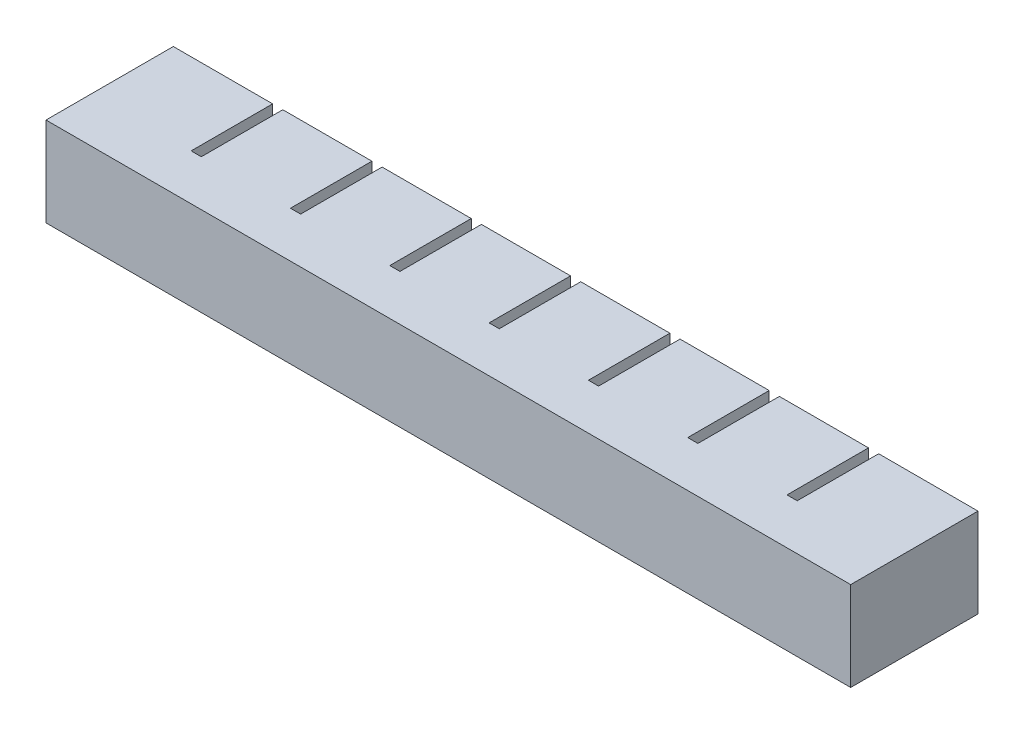
SolidWorks part; units mm, degrees
ref_plane "Front Plane" through (0, 0, 0) normal (0, 0, 1) x (1, 0, 0)
ref_plane "Top Plane" through (0, 0, 0) normal (0, 1, 0) x (1, 0, 0)
ref_plane "Right Plane" through (0, 0, 0) normal (1, 0, 0) x (0, 0, -1)
sketch "Sketch1" plane through (0, 0, 0) normal (0, 0, 1) x (1, 0, 0)
  line L1 (0, 0) -> (17.5, 0)
  line L2 (0, 0) -> (0, 17.5)
  line L3 (0, 17.5) -> (17.5, 17.5)
  line L4 (17.5, 0) -> (17.5, 17.5)
  dimension "D1" = 17.5
  dimension "D2" = 17.5
extrude "Boss-Extrude1" add sketch "Sketch1" along normal blind 20
sketch "Sketch2" plane through (0, 0, 20) normal (0, 0, 1) x (1, 0, 0)
  line L0 (0, 0) -> (17.5, 0) construction
  line L1 (3, 14.5) -> (14.5, 14.5)
  line L2 (3, 14.5) -> (3, 3)
  line L3 (3, 3) -> (14.5, 3)
  line L4 (14.5, 14.5) -> (14.5, 3)
  line L5 (17.5, 0) -> (17.5, 17.5) construction
  line L6 (17.5, 17.5) -> (0, 17.5) construction
  line L7 (0, 17.5) -> (0, 0) construction
  dimension "D1" = 3
  dimension "D2" = 3
  dimension "D3" = 3
  dimension "D4" = 3
extrude "Cut-Extrude1" cut sketch "Sketch2" against normal blind 17
sketch "Sketch4" plane through (0, 0, 0) normal (-1, 0, 0) x (0, 0, 1)
  line L0 (20, 17.5) -> (0, 17.5) construction
  line L1 (20, 0) -> (16, 0)
  line L2 (20, 0) -> (20, 17.5)
  line L3 (20, 17.5) -> (16, 17.5)
  line L4 (16, 0) -> (16, 17.5)
  dimension "D1" = 4
extrude "Boss-Extrude2" add sketch "Sketch4" along normal blind 2
pattern_linear "LPattern1" count 8 spacing 19.5 along (-1, 0, 0) of bodies 103
combine bodies "Combine1" operation type add bodies to combine 107 108 109 110 104 105 103 106
sketch "Sketch5" plane through (-136.5, 0, 0) normal (-1, 0, 0) x (0, 0, 1)
  line L1 (16, 0) -> (0, 0)
  line L2 (16, 0) -> (16, 17.5)
  line L3 (16, 17.5) -> (0, 17.5)
  line L4 (0, 0) -> (0, 17.5)
extrude "Boss-Extrude3" add sketch "Sketch5" along normal up to surface (2 mm away) up to face at (-138.5, 8.75, 18)
sketch "Sketch6" plane through (17.5, 0, 0) normal (1, 0, 0) x (0, 0, -1)
  line L1 (0, 17.5) -> (-20, 17.5)
  line L2 (0, 17.5) -> (0, 0)
  line L3 (0, 0) -> (-20, 0)
  line L4 (-20, 17.5) -> (-20, 0)
extrude "Boss-Extrude4" add sketch "Sketch6" along normal blind 2
ref_point "Point1"
sketch "Sketch7" plane through (0, 0, 20) normal (0, 0, 1) x (1, 0, 0)
  line L0 (-122, 3) -> (-122, 14.5) construction
  line L1 (3, 7.5) -> (-122, 7.5)
  line L2 (3, 7.5) -> (3, 10)
  line L3 (3, 10) -> (-122, 10)
  line L4 (-122, 7.5) -> (-122, 10)
  line L5 (3, 7.5) -> (-122, 10) construction
  line L6 (3, 10) -> (-122, 7.5) construction
  point P0 (-59.5, 8.75)
  dimension "D1" = 2.5
extrude "Cut-Extrude2" cut sketch "Sketch7" against normal blind 2
sketch "Sketch8" plane through (0, 0, 20) normal (0, 0, 1) x (1, 0, 0)
  line L0 (-138.5, 0) -> (19.5, 0) construction
  line L1 (16.8155, 2) -> (-135.8155, 2)
  line L2 (16.8155, 2) -> (16.8155, 15.5)
  line L3 (16.8155, 15.5) -> (-135.8155, 15.5)
  line L4 (-135.8155, 2) -> (-135.8155, 15.5)
  line L5 (16.8155, 2) -> (-135.8155, 15.5) construction
  line L6 (16.8155, 15.5) -> (-135.8155, 2) construction
  line L19 (18.5, 16.5) -> (-137.5, 16.5)
  line L20 (-137.5, 16.5) -> (-137.5, 1)
  line L21 (-137.5, 1) -> (18.5, 1)
  line L22 (18.5, 1) -> (18.5, 16.5)
  line L23 (18.5, 16.5) -> (-137.5, 16.5)
  line L24 (-137.5, 16.5) -> (-137.5, 1)
  line L25 (-137.5, 1) -> (18.5, 1)
  line L26 (18.5, 1) -> (18.5, 16.5)
  point P0 (-59.5, 8.75)
  dimension "D1" = 2
  dimension "D2" = 1
extrude "Boss-Extrude5" add sketch "Sketch8" along normal blind 2
sketch "Sketch9" plane through (0, 0, 20) normal (0, 0, 1) x (1, 0, 0)
  line L1 (18.5, 1) -> (-137.5, 1)
  line L2 (18.5, 1) -> (18.5, 16.5)
  line L3 (18.5, 16.5) -> (-137.5, 16.5)
  line L4 (-137.5, 1) -> (-137.5, 16.5)
extrude "Boss-Extrude6" add sketch "Sketch9" along normal blind 2
sketch "Sketch10" plane through (0, 0, 20) normal (0, 0, 1) x (1, 0, 0)
  line L1 (19.5, 0) -> (-138.5, 0)
  line L2 (19.5, 0) -> (19.5, 17.5)
  line L3 (19.5, 17.5) -> (-138.5, 17.5)
  line L4 (-138.5, 0) -> (-138.5, 17.5)
extrude "Boss-Extrude7" add sketch "Sketch10" along normal blind 5
